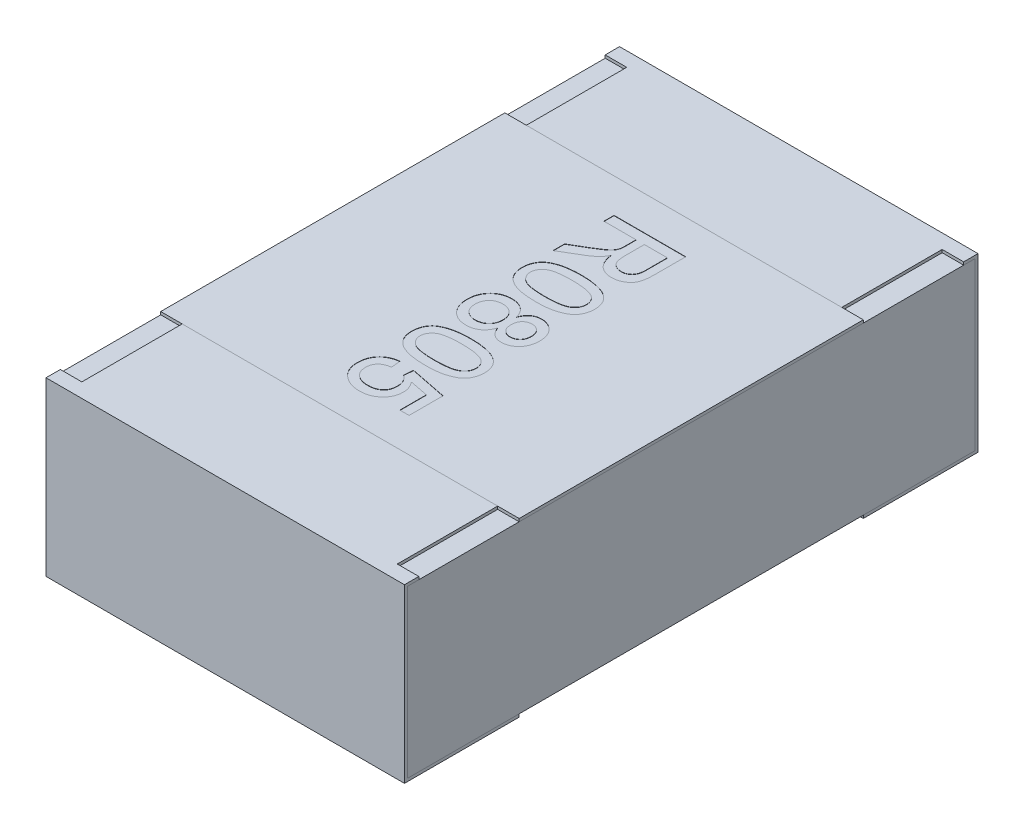
SolidWorks part; units mm, degrees
ref_plane "Front Plane" through (0, 0, 0) normal (0, 0, 1) x (1, 0, 0)
ref_plane "Top Plane" through (0, 0, 0) normal (0, 1, 0) x (1, 0, 0)
ref_plane "Right Plane" through (0, 0, 0) normal (1, 0, 0) x (0, 0, -1)
sketch "Sketch4" plane through (0, 0, 0) normal (1, 0, 0) x (0, 0, -1)
  line L0 (0, 0.1169) -> (0, -0.0721) construction
  line L1 (-1, 0) -> (0.3788, 0) construction
  line L2 (-1, 0.3) -> (-1, -0.3)
  line L3 (-1, -0.3) -> (-0.6, -0.3)
  line L4 (-0.6, 0.3) -> (-0.6, 0.29)
  line L5 (-0.6, 0.29) -> (-0.99, 0.29)
  line L6 (-0.99, 0.29) -> (-0.99, -0.29)
  line L7 (-0.99, -0.29) -> (-0.6, -0.29)
  line L8 (-0.6, -0.29) -> (-0.6, -0.3)
  line L9 (-0.6, 0.3) -> (-1, 0.3)
  line L10 (0.6, 0.3) -> (1, 0.3)
  line L11 (0.6, -0.29) -> (0.6, -0.3)
  line L12 (0.99, -0.29) -> (0.6, -0.29)
  line L13 (0.99, 0.29) -> (0.99, -0.29)
  line L14 (0.6, 0.29) -> (0.99, 0.29)
  line L15 (0.6, 0.3) -> (0.6, 0.29)
  line L16 (1, -0.3) -> (0.6, -0.3)
  line L17 (1, 0.3) -> (1, -0.3)
  dimension "LENGTH" = 1
  dimension "HEIGHT" = 0.6
  dimension "END CAP TOP LENGTH" = 0.4
  dimension "END CAP BOTTOM LENGTH" = 0.4
  dimension "D5" = 0.01
  dimension "D6" = 0.01
extrude "Boss-Extrude2" add sketch "Sketch4" along normal mid plane 1.25
sketch "Sketch5" plane through (0, 0, 0) normal (1, 0, 0) x (0, 0, -1)
  line L1 (-0.99, 0.29) -> (0.99, 0.29)
  line L2 (-0.99, 0.29) -> (-0.99, -0.29)
  line L3 (-0.99, -0.29) -> (0.99, -0.29)
  line L4 (0.99, 0.29) -> (0.99, -0.29)
extrude "Boss-Extrude3" add sketch "Sketch5" along normal up to surface and the other way up to surface separate body
sketch "Sketch6" plane through (0, 0.3, 0) normal (0, 1, 0) x (1, 0, 0)
  line L0 (-0.625, 1) -> (-0.625, 0.6) construction
  line L1 (-0.625, 0.95) -> (-0.55, 0.95)
  line L2 (-0.625, 0.95) -> (-0.625, 0.6)
  line L3 (-0.625, 0.6) -> (-0.55, 0.6)
  line L4 (-0.55, 0.95) -> (-0.55, 0.6)
  line L5 (0.625, 0.6) -> (-0.625, 0.6) construction
  line L6 (0, 0.0345) -> (0, -0.0345) construction
  line L7 (-0.0325, 0) -> (0.03, 0) construction
  line L8 (0.625, 0.95) -> (0.625, 0.6)
  line L9 (0.625, 0.6) -> (0.55, 0.6)
  line L10 (0.55, 0.95) -> (0.55, 0.6)
  line L11 (0.625, 0.95) -> (0.55, 0.95)
  line L12 (0.625, -0.95) -> (0.55, -0.95)
  line L13 (0.625, -0.95) -> (0.625, -0.6)
  line L14 (0.625, -0.6) -> (0.55, -0.6)
  line L15 (0.55, -0.95) -> (0.55, -0.6)
  line L16 (-0.625, -0.95) -> (-0.55, -0.95)
  line L17 (-0.625, -0.95) -> (-0.625, -0.6)
  line L18 (-0.625, -0.6) -> (-0.55, -0.6)
  line L19 (-0.55, -0.95) -> (-0.55, -0.6)
  dimension "TOP CUT WIDTH" = 0.075
  dimension "TOP CUT LENGTH" = 0.35
extrude "Cut-Extrude1" cut sketch "Sketch6" against normal up to surface (0.01 mm away) up to face at (0, 0.29, 0)
sketch "Sketch7" plane through (0, 0.29, 0) normal (0, 1, 0) x (1, 0, 0)
  line L1 (-0.625, 0.6) -> (0.625, 0.6)
  line L2 (-0.625, 0.6) -> (-0.625, -0.6)
  line L3 (-0.625, -0.6) -> (0.625, -0.6)
  line L4 (0.625, 0.6) -> (0.625, -0.6)
  line L5 (0.55, -0.6) -> (-0.55, -0.6) construction
  line L6 (0.55, 0.6) -> (-0.55, 0.6) construction
  line L7 (-0.625, -0.99) -> (-0.625, 0.99) construction
  line L8 (0.625, 0.99) -> (0.625, -0.99) construction
extrude "Boss-Extrude4" add sketch "Sketch7" along normal up to surface (0.01 mm away) separate body up to face at (0, 0.3, -0.875)
sketch "Sketch11" plane through (0, 0.3, 0) normal (0, 1, 0) x (1, 0, 0)
  line L0 (0, 0) -> (-0.125, 0) construction
  line L1 (-0.125, 0.515) -> (-0.125, -0.515) construction
  text T0 "R0805" font "Arial" height 0.25
  dimension "D1" = 0.125
extrude "TEXT0805" cut sketch "Sketch11" against normal blind 0.001
